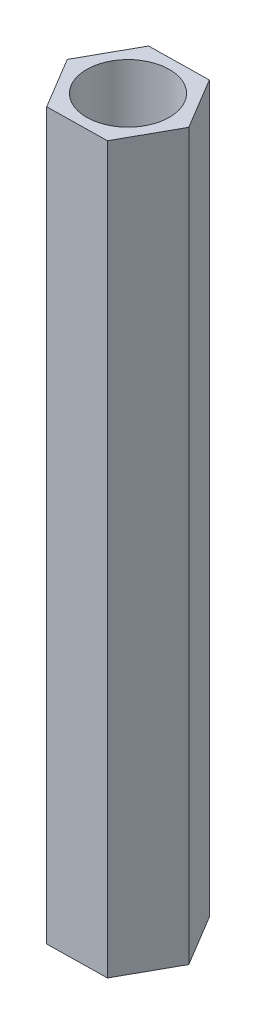
SolidWorks part; units mm, degrees
material "黄铜"
ref_plane "前视基准面" through (0, 0, 0) normal (0, 0, 1) x (1, 0, 0)
ref_plane "上视基准面" through (0, 0, 0) normal (0, 1, 0) x (1, 0, 0)
ref_plane "右视基准面" through (0, 0, 0) normal (1, 0, 0) x (0, 0, -1)
sketch "草图1" plane through (0, 0, 0) normal (0, 1, 0) x (1, 0, 0)
  line L1 (1.4019, 2.5235) -> (-1.4844, 2.4758)
  line L2 (-1.4844, 2.4758) -> (-2.8864, -0.0476)
  line L3 (-2.8864, -0.0476) -> (-1.4019, -2.5235)
  line L4 (-1.4019, -2.5235) -> (1.4844, -2.4758)
  line L5 (1.4844, -2.4758) -> (2.8864, 0.0476)
  line L6 (2.8864, 0.0476) -> (1.4019, 2.5235)
  circle A0 centre (0, 0) radius 2.5 construction
  circle A1 centre (0, 0) radius 2
extrude "凸台-拉伸1" add sketch "草图1" along normal blind 35
